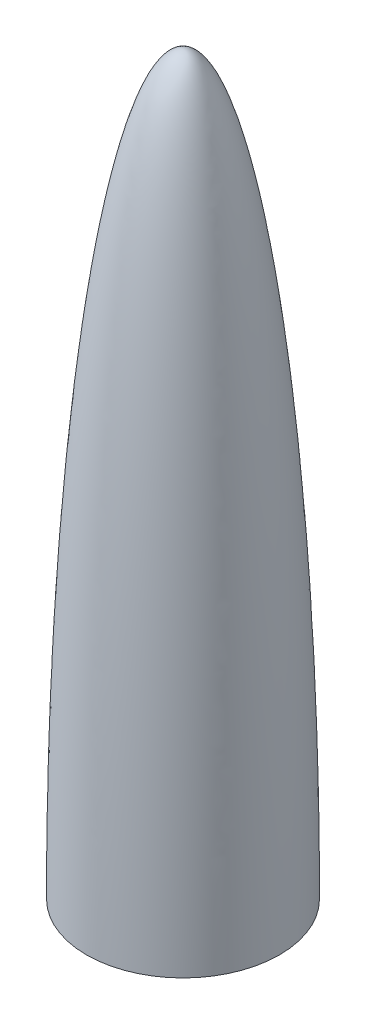
SolidWorks part; units mm, degrees
ref_plane "Alzado" through (0, 0, 0) normal (0, 0, 1) x (1, 0, 0)
ref_plane "Planta" through (0, 0, 0) normal (0, 1, 0) x (1, 0, 0)
ref_plane "Vista lateral" through (0, 0, 0) normal (1, 0, 0) x (0, 0, -1)
sketch "Croquis1" plane through (0, 0, 0) normal (0, 0, 1) x (1, 0, 0)
  line L0 (40, 0) -> (-40, 0) construction
  line L1 (0, 0) -> (0, 303.8)
  line L2 (40, 0) -> (38.8, 0)
  line L3 (0, 305) -> (0, 303.8)
  ellipse E0 centre (0, 0) end of major axis (0, 305) minor radius 40 (40, 0) -> (0, 305) ccw
  spline S0 degree 1 poles (38.8, 0) (0, 303.8) knots 0 0 1 1 construction
  spline S1 degree 3 poles (38.8, 0) (38.8, 9.9601) (38.6715, 29.9352) (38.0949, 59.5651) (37.14, 88.632) (35.3752, 126.2446) (32.2774, 170.4384) (27.2759, 216.9056) (22.2007, 248.6581) (17.7194, 269.1357) (14.1848, 281.8799) (10.5212, 291.8708) (7.4117, 297.7954) (4.9599, 301.0309) (3.1828, 302.6959) (1.5095, 303.6164) (0.523, 303.8) (0, 303.8) knots -1.570796 -1.570796 -1.570796 -1.570796 -1.472622 -1.374447 -1.276272 -1.178097 -0.981748 -0.785398 -0.589049 -0.490874 -0.392699 -0.294524 -0.19635 -0.147262 -0.098175 -0.049087 0 0 0 0
  point P4 (0, 0)
  dimension "D1" = 80
  dimension "D2" = 305
  dimension "D3" = 1.2
revolve "Revolución1" add sketch "Croquis1" angle 360 about L1
